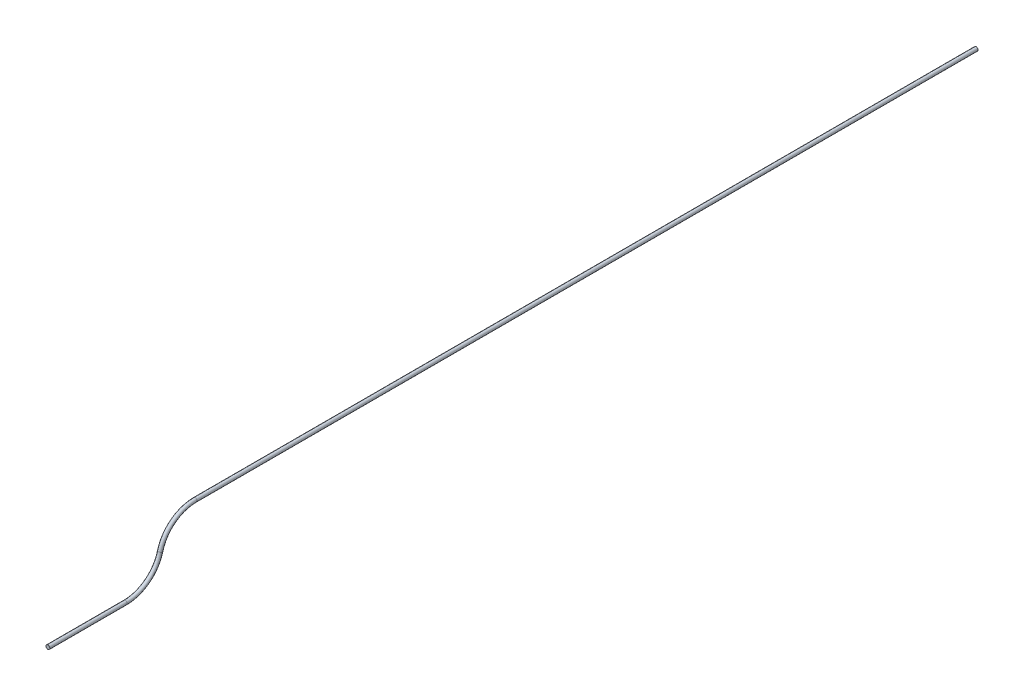
SolidWorks part; units mm, degrees
ref_plane "Front Plane" through (0, 0, 0) normal (0, 0, 1) x (1, 0, 0)
ref_plane "Top Plane" through (0, 0, 0) normal (0, 1, 0) x (1, 0, 0)
ref_plane "Right Plane" through (0, 0, 0) normal (1, 0, 0) x (0, 0, -1)
sketch "Sketch1" plane through (0, 0, 0) normal (0, 0, 1) x (1, 0, 0)
  circle A0 centre (0, 0) radius 4.0323
  dimension "D1" = 8.0645
sketch "Sketch2" plane through (0, 0, 0) normal (1, 0, 0) x (0, 0, -1)
  line L0 (0, 0) -> (163.5, 0)
  line L1 (311.0607, 114.3) -> (1962.0607, 114.3)
  arc A0 (163.5, 0) -> (237.2803, 57.15) centre (163.5, 76.2) ccw
  arc A1 (237.2803, 57.15) -> (311.0607, 114.3) centre (311.0607, 38.1) cw
  dimension "D3" = 76.2
  dimension "D4" = 76.2
  dimension "D1" = 163.5
  dimension "D2" = 114.3
  dimension "D5" = 1651
sweep "Sweep1" add profiles "Sketch1" path "Sketch2"
